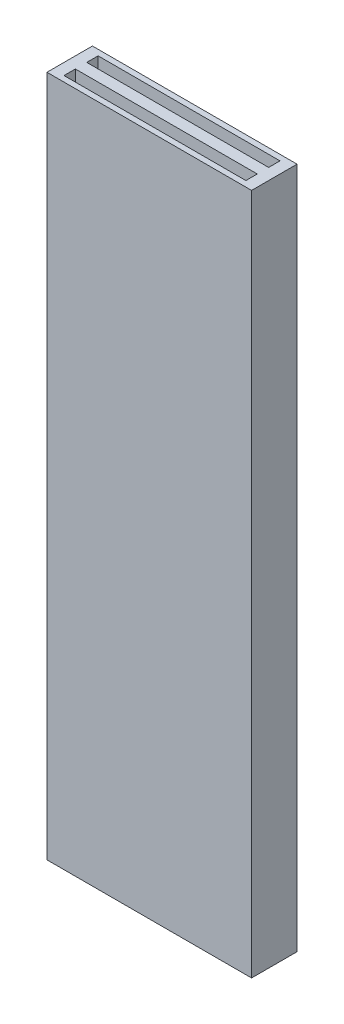
SolidWorks part; units mm, degrees
ref_plane "Front Plane" through (0, 0, 0) normal (0, 0, 1) x (1, 0, 0)
ref_plane "Top Plane" through (0, 0, 0) normal (0, 1, 0) x (1, 0, 0)
ref_plane "Right Plane" through (0, 0, 0) normal (1, 0, 0) x (0, 0, -1)
sketch "Sketch1" plane through (0, 0, 0) normal (0, 1, 0) x (1, 0, 0)
  line L1 (-4.5, -1) -> (4.5, -1)
  line L2 (-4.5, -1) -> (-4.5, 1)
  line L3 (-4.5, 1) -> (4.5, 1)
  line L4 (4.5, -1) -> (4.5, 1)
  line L5 (-4.5, -1) -> (4.5, 1) construction
  line L6 (-4.5, 1) -> (4.5, -1) construction
  point P0 (0, 0)
  dimension "D1" = 9
  dimension "D2" = 2
extrude "Boss-Extrude1" add sketch "Sketch1" along normal mid plane 30
sketch "Sketch2" plane through (0, 15, 0) normal (0, 1, 0) x (1, 0, 0)
  line L1 (-4, 0.25) -> (4, 0.25)
  line L2 (-4, 0.25) -> (-4, 0.75)
  line L3 (-4, 0.75) -> (4, 0.75)
  line L4 (4, 0.25) -> (4, 0.75)
  line L5 (-4, 0.25) -> (4, 0.75) construction
  line L6 (-4, 0.75) -> (4, 0.25) construction
  point P0 (0, 0.5)
  dimension "D1" = 0.5
  dimension "D2" = 8
  dimension "D3" = 0
  dimension "D4" = 0.5
extrude "Cut-Extrude1" cut sketch "Sketch2" against normal through all and the other way through all
mirror "Mirror1" about plane through (0, 0, 0) normal (0, 0, 1) of "Cut-Extrude1"
